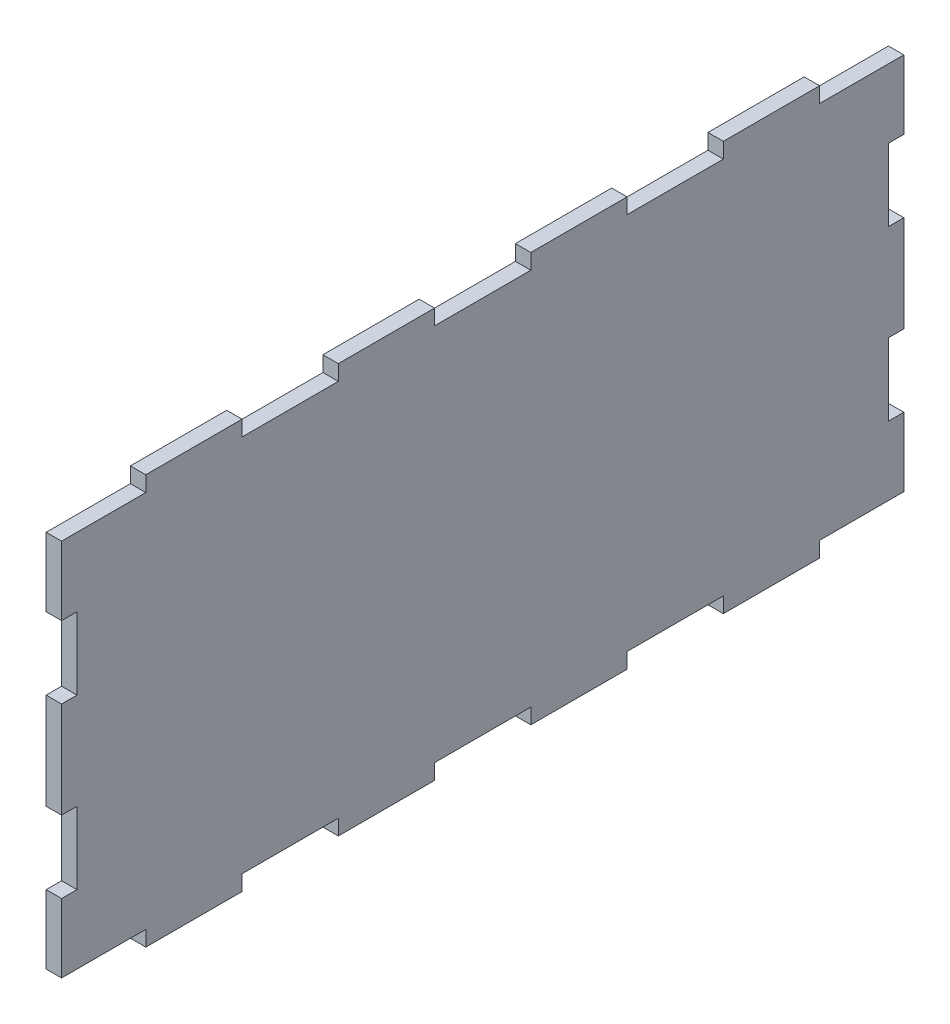
SolidWorks part; units mm, degrees
ref_plane "Front Plane" through (0, 0, 0) normal (0, 0, 1) x (1, 0, 0)
ref_plane "Top Plane" through (0, 0, 0) normal (0, 1, 0) x (1, 0, 0)
ref_plane "Right Plane" through (0, 0, 0) normal (1, 0, 0) x (0, 0, -1)
sketch "Sketch1" plane through (0, 0, 0) normal (1, 0, 0) x (0, 0, -1)
  line L0 (-10, 42.5) -> (-30, 42.5)
  line L1 (0, 55) -> (0, -55) construction
  line L2 (-87.5, 39.3) -> (-87.5, 25)
  line L3 (55, 0) -> (-55, 0) construction
  line L4 (0, 0) -> (-87.5, 0) construction
  line L5 (-87.5, 10) -> (-84.3, 10)
  line L6 (-84.3, 10) -> (-84.3, 25)
  line L7 (-84.3, 25) -> (-87.5, 25)
  line L8 (-87.5, 10) -> (-87.5, -10)
  line L9 (-87.5, 39.3) -> (-70, 39.3)
  line L10 (-70, 39.3) -> (-70, 42.5)
  line L11 (-50, 42.5) -> (-50, 39.3)
  line L12 (-50, 39.3) -> (-30, 39.3)
  line L13 (-30, 39.3) -> (-30, 42.5)
  line L14 (-10, 42.5) -> (-10, 39.3)
  line L15 (-10, 39.3) -> (10, 39.3)
  line L16 (-50, 42.5) -> (-70, 42.5)
  line L17 (0, 0) -> (0, 39.3) construction
  line L18 (-10, -39.3) -> (10, -39.3)
  line L19 (-50, -42.5) -> (-70, -42.5)
  line L20 (-10, -42.5) -> (-10, -39.3)
  line L21 (-30, -39.3) -> (-30, -42.5)
  line L22 (-50, -39.3) -> (-30, -39.3)
  line L23 (-50, -42.5) -> (-50, -39.3)
  line L24 (-70, -39.3) -> (-70, -42.5)
  line L25 (-87.5, -39.3) -> (-70, -39.3)
  line L26 (-84.3, -25) -> (-87.5, -25)
  line L27 (-84.3, -10) -> (-84.3, -25)
  line L28 (-87.5, -10) -> (-84.3, -10)
  line L29 (-87.5, -39.3) -> (-87.5, -25)
  line L30 (-10, -42.5) -> (-30, -42.5)
  line L31 (10, -42.5) -> (30, -42.5)
  line L32 (87.5, -39.3) -> (87.5, -25)
  line L33 (87.5, -10) -> (84.3, -10)
  line L34 (84.3, -10) -> (84.3, -25)
  line L35 (84.3, -25) -> (87.5, -25)
  line L36 (87.5, -39.3) -> (70, -39.3)
  line L37 (70, -39.3) -> (70, -42.5)
  line L38 (50, -42.5) -> (50, -39.3)
  line L39 (50, -39.3) -> (30, -39.3)
  line L40 (30, -39.3) -> (30, -42.5)
  line L41 (10, -42.5) -> (10, -39.3)
  line L42 (50, -42.5) -> (70, -42.5)
  line L43 (50, 42.5) -> (70, 42.5)
  line L44 (10, 42.5) -> (10, 39.3)
  line L45 (30, 39.3) -> (30, 42.5)
  line L46 (50, 39.3) -> (30, 39.3)
  line L47 (50, 42.5) -> (50, 39.3)
  line L48 (70, 39.3) -> (70, 42.5)
  line L49 (87.5, 39.3) -> (70, 39.3)
  line L50 (87.5, 10) -> (87.5, -10)
  line L51 (84.3, 25) -> (87.5, 25)
  line L52 (84.3, 10) -> (84.3, 25)
  line L53 (87.5, 10) -> (84.3, 10)
  line L54 (87.5, 39.3) -> (87.5, 25)
  line L55 (10, 42.5) -> (30, 42.5)
  point P36 (0, -39.3)
  dimension "D1" = 87.5
  dimension "D2" = 10
  dimension "D3" = 3.2
  dimension "D4" = 15
  dimension "D5" = 10
  dimension "D6" = 3.2
  dimension "D7" = 20
  dimension "D8" = 20
  dimension "D9" = 20
  dimension "D10" = 42.5
extrude "Boss-Extrude1" add sketch "Sketch1" along normal blind 3.2
